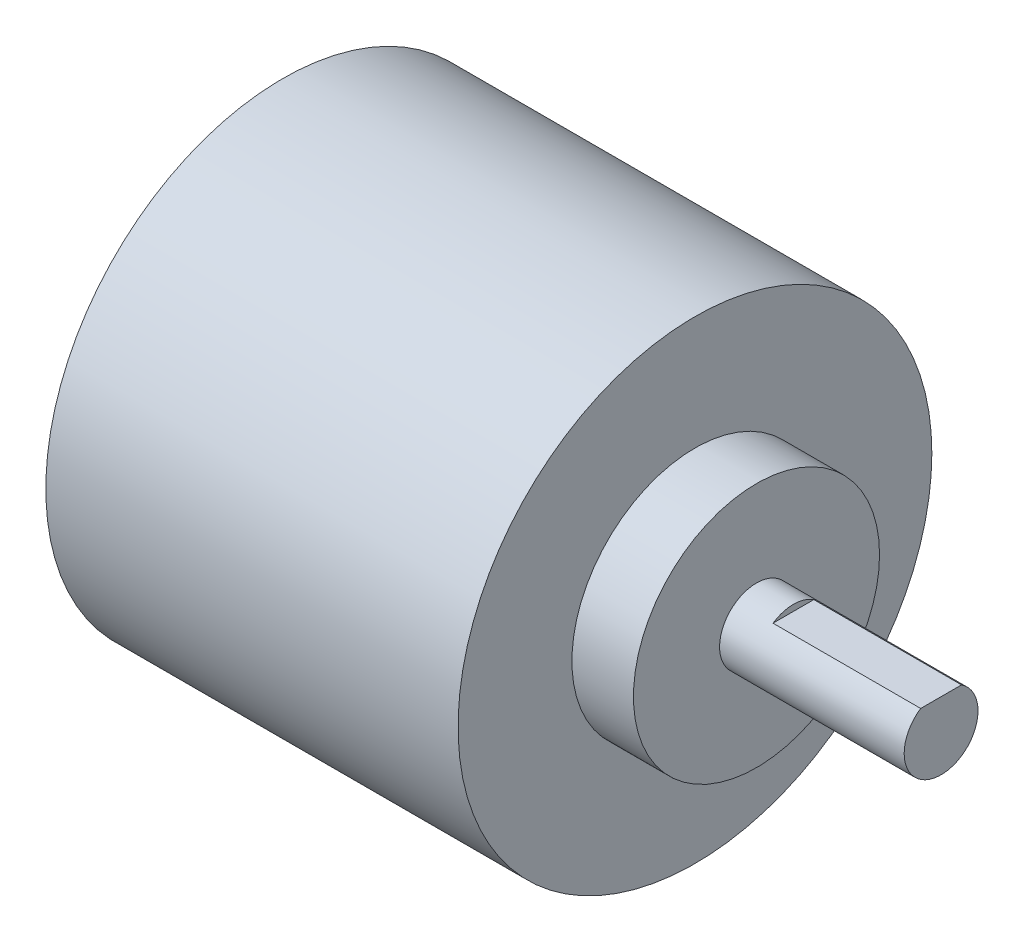
SolidWorks part; units mm, degrees
ref_plane "Plan de face" through (0, 0, 0) normal (0, 0, 1) x (1, 0, 0)
ref_plane "Plan de dessus" through (0, 0, 0) normal (0, 1, 0) x (1, 0, 0)
ref_plane "Plan de droite" through (0, 0, 0) normal (1, 0, 0) x (0, 0, -1)
sketch "esquisse_base_codeur" plane through (0, 0, 0) normal (1, 0, 0) x (0, 0, -1)
  circle A0 centre (0, 0) radius 19.25
  dimension "D1" = 38.5
extrude "base_codeur" add sketch "esquisse_base_codeur" along normal blind 33.5
sketch "esquisse_plateau_codeur" plane through (33.5, 0, 0) normal (1, 0, 0) x (0, 0, -1)
  circle A0 centre (0, 0) radius 10
  dimension "D1" = 20
extrude "plateau_codeur" add sketch "esquisse_plateau_codeur" along normal blind 5
sketch "esquisse_arbre" plane through (38.5, 0, 0) normal (1, 0, 0) x (0, 0, -1)
  circle A0 centre (0, 0) radius 3
  dimension "D1" = 6
extrude "arbre" add sketch "esquisse_arbre" along normal blind 15
sketch "esquisse_usinage_arbre" plane through (53.5, 0, 0) normal (1, 0, 0) x (0, 0, -1)
  line L0 (0, 0) -> (0, 3) construction
  line L2 (-1.6583, 2.5) -> (1.6583, 2.5)
  circle A0 centre (0, 0) radius 3 construction
  arc A1 (1.6583, 2.5) -> (-1.6583, 2.5) centre (0, 0) ccw
  dimension "D1" = 0.5
extrude "usinage_arbre" cut sketch "esquisse_usinage_arbre" against normal blind 12
